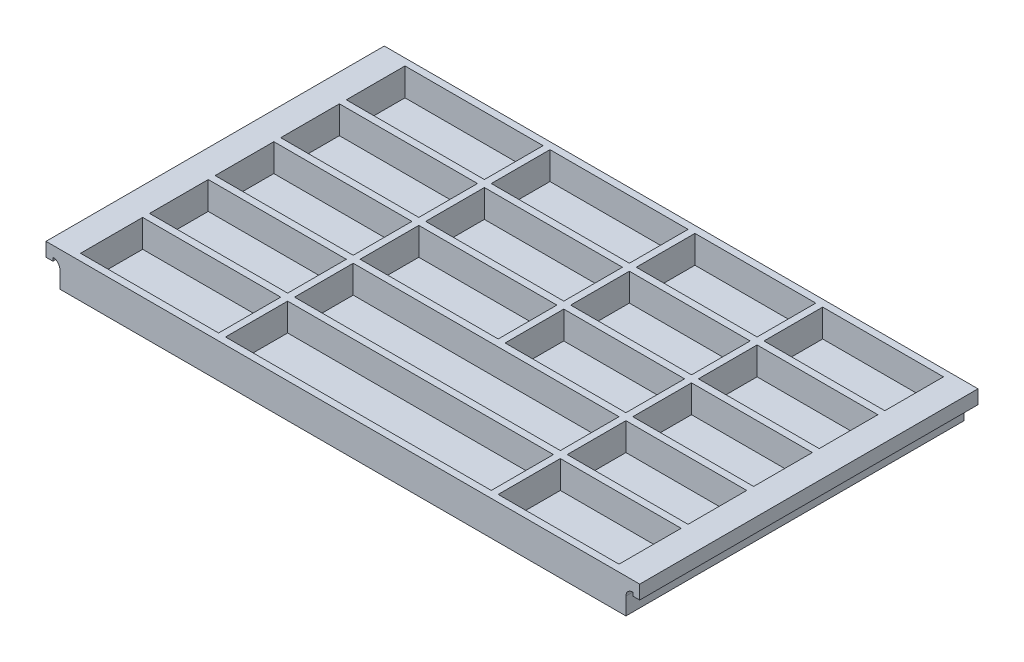
SolidWorks part; units mm, degrees
ref_plane "Front Plane" through (0, 0, 0) normal (0, 0, 1) x (1, 0, 0)
ref_plane "Top Plane" through (0, 0, 0) normal (0, 1, 0) x (1, 0, 0)
ref_plane "Right Plane" through (0, 0, 0) normal (1, 0, 0) x (0, 0, -1)
sketch "Sketch1" plane through (0, 0, 0) normal (0, 1, 0) x (1, 0, 0)
  line L1 (101.6, -62.23) -> (-101.6, -62.23)
  line L2 (101.6, -62.23) -> (101.6, 62.23)
  line L3 (101.6, 62.23) -> (-101.6, 62.23)
  line L4 (-101.6, -62.23) -> (-101.6, 62.23)
  line L5 (101.6, -62.23) -> (-101.6, 62.23) construction
  line L6 (101.6, 62.23) -> (-101.6, -62.23) construction
  line L32 (99.06, -59.69) -> (99.06, -36.83)
  line L37 (99.06, 59.69) -> (54.61, 59.69)
  line L39 (-99.06, -59.69) -> (-99.06, -36.83)
  line L41 (99.06, -59.69) -> (54.61, -59.69)
  line L42 (-48.26, 59.69) -> (-48.26, 38.1)
  line L45 (54.61, 59.69) -> (54.61, 38.1)
  line L46 (-99.06, 38.1) -> (-48.26, 38.1)
  line L51 (-99.06, 13.97) -> (-48.26, 13.97)
  line L53 (-44.4712, -27.2386) -> (-44.3417, -27.2342)
  line L54 (-99.06, -10.16) -> (-48.26, -10.16)
  line L55 (-99.06, -34.29) -> (-48.26, -34.29)
  line L56 (-45.72, 59.69) -> (-45.72, 38.1)
  line L57 (52.07, 59.69) -> (52.07, 38.1)
  line L60 (5.08, 59.69) -> (5.08, 38.1)
  line L61 (-99.06, 35.56) -> (-48.26, 35.56)
  line L62 (-99.06, 11.43) -> (-48.26, 11.43)
  line L63 (-99.06, -12.7) -> (-48.26, -12.7)
  line L64 (-99.06, -36.83) -> (-48.26, -36.83)
  line L66 (7.62, 59.69) -> (7.62, 38.1)
  line L71 (7.62, 35.56) -> (7.62, 13.97)
  line L73 (5.08, 35.56) -> (5.08, 13.97)
  line L76 (-48.26, 59.69) -> (-99.06, 59.69)
  line L78 (99.06, 59.69) -> (-99.06, 59.69) construction
  line L79 (-45.72, 35.56) -> (-45.72, 13.97)
  line L81 (-45.72, 59.69) -> (-45.72, -59.69) construction
  line L82 (-48.26, 35.56) -> (-48.26, 13.97)
  line L83 (5.08, 59.69) -> (-45.72, 59.69)
  line L84 (-48.26, 59.69) -> (-48.26, -59.69) construction
  line L85 (7.62, 38.1) -> (52.07, 38.1)
  line L86 (7.62, 35.56) -> (52.07, 35.56)
  line L87 (-99.06, 38.1) -> (99.06, 38.1) construction
  line L88 (-48.26, 11.43) -> (-48.26, -10.16)
  line L89 (-99.06, 35.56) -> (99.06, 35.56) construction
  line L90 (-45.72, 13.97) -> (5.08, 13.97)
  line L92 (-99.06, 13.97) -> (99.06, 13.97) construction
  line L93 (-45.72, 11.43) -> (-45.72, -10.16)
  line L94 (-45.72, 11.43) -> (5.08, 11.43)
  line L96 (-99.06, 11.43) -> (99.06, 11.43) construction
  line L97 (-99.06, 13.97) -> (-99.06, 35.56)
  line L99 (-99.06, -59.69) -> (-99.06, 59.69) construction
  line L100 (-99.06, 38.1) -> (-99.06, 59.69)
  line L101 (-99.06, -10.16) -> (-99.06, 11.43)
  line L102 (-45.72, -12.7) -> (-45.72, -34.29)
  line L103 (-45.72, -10.16) -> (5.08, -10.16)
  line L104 (-48.26, -12.7) -> (-48.26, -34.29)
  line L105 (-99.06, -10.16) -> (99.06, -10.16) construction
  line L106 (-45.72, -12.7) -> (5.08, -12.7)
  line L107 (-45.72, 35.56) -> (5.08, 35.56)
  line L108 (-99.06, -12.7) -> (99.06, -12.7) construction
  line L109 (-45.72, 38.1) -> (5.08, 38.1)
  line L110 (-45.72, -34.29) -> (5.08, -34.29)
  line L111 (-48.26, -36.83) -> (-48.26, -59.69)
  line L112 (-99.06, -34.29) -> (99.06, -34.29) construction
  line L113 (-45.72, -36.83) -> (-45.72, -59.69)
  line L114 (-45.72, -36.83) -> (52.07, -36.83)
  line L115 (-99.06, -34.29) -> (-99.06, -12.7)
  line L116 (-99.06, -36.83) -> (99.06, -36.83) construction
  line L117 (-48.26, -59.69) -> (-99.06, -59.69)
  line L118 (52.07, -59.69) -> (-45.72, -59.69)
  line L119 (99.06, -59.69) -> (-99.06, -59.69) construction
  line L120 (54.61, -36.83) -> (99.06, -36.83)
  line L121 (52.07, -36.83) -> (52.07, -59.69)
  line L122 (54.61, -36.83) -> (54.61, -59.69)
  line L123 (52.07, 59.69) -> (52.07, -59.69) construction
  line L124 (54.61, -34.29) -> (99.06, -34.29)
  line L125 (54.61, 59.69) -> (54.61, -59.69) construction
  line L126 (99.06, -34.29) -> (99.06, -12.7)
  line L127 (99.06, -10.16) -> (99.06, 11.43)
  line L128 (99.06, -59.69) -> (99.06, 59.69) construction
  line L129 (54.61, -12.7) -> (54.61, -34.29)
  line L130 (52.07, -12.7) -> (52.07, -34.29)
  line L131 (54.61, -10.16) -> (99.06, -10.16)
  line L132 (54.61, -12.7) -> (99.06, -12.7)
  line L133 (99.06, 13.97) -> (99.06, 35.56)
  line L134 (99.06, 38.1) -> (99.06, 59.69)
  line L135 (54.61, 35.56) -> (99.06, 35.56)
  line L136 (52.07, 35.56) -> (52.07, 13.97)
  line L137 (54.61, 35.56) -> (54.61, 13.97)
  line L138 (54.61, 38.1) -> (99.06, 38.1)
  line L139 (52.07, 59.69) -> (7.62, 59.69)
  line L140 (54.61, 13.97) -> (99.06, 13.97)
  line L141 (52.07, 11.43) -> (52.07, -10.16)
  line L142 (54.61, 11.43) -> (54.61, -10.16)
  line L143 (54.61, 11.43) -> (99.06, 11.43)
  line L144 (5.08, -12.7) -> (52.07, -12.7)
  line L145 (5.08, -34.29) -> (52.07, -34.29)
  line L146 (7.62, 13.97) -> (52.07, 13.97)
  line L147 (5.08, 11.43) -> (5.08, -10.16)
  line L148 (7.62, 11.43) -> (7.62, -10.16)
  line L149 (7.62, 11.43) -> (52.07, 11.43)
  line L150 (7.62, -10.16) -> (52.07, -10.16)
  point P0 (0, 0)
  point P6 (-109.855, 31.75)
  point P7 (109.855, 31.75)
  point P8 (-109.855, 1.27)
  point P9 (109.855, 1.27)
  point P10 (-109.855, -29.21)
  point P11 (109.855, -29.21)
  point P12 (-109.855, -26.67)
  point P13 (109.855, -26.67)
  point P14 (107.315, -59.69)
  point P15 (-107.315, -59.69)
  point P16 (-107.315, 59.69)
  point P17 (107.315, 59.69)
  point P18 (-109.855, 3.81)
  point P19 (109.855, 3.81)
  point P20 (-109.855, 34.29)
  point P21 (109.855, 34.29)
  point P74 (-66.675, 62.23)
  point P75 (-48.26, 34.29)
  point P80 (-64.135, 62.23)
  point P81 (-23.495, 62.23)
  point P86 (-23.495, 34.29)
  point P87 (19.685, 62.23)
  point P88 (19.685, 34.29)
  point P89 (62.865, 62.23)
  point P90 (54.61, 34.29)
  point P91 (-64.135, 34.29)
  point P92 (-20.955, 62.23)
  point P93 (-20.955, 34.29)
  point P94 (22.225, 62.23)
  point P95 (22.225, 34.29)
  point P96 (65.405, 62.23)
  point P97 (57.15, 38.1)
  dimension "D1" = 203.2
  dimension "D2" = 124.46
  dimension "D3" = 2.54
  dimension "D4" = 4
  dimension "D5" = 21.59
  dimension "D6" = 21.59
  dimension "D7" = 50.8
  dimension "D8" = 44.45
  dimension "D9" = 2.54
  dimension "D10" = 2.54
  dimension "D11" = 2.54
  dimension "D13" = 2.54
  dimension "D15" = 2.54
  dimension "D16" = 2.54
  dimension "D17" = 50.8
  dimension "D18" = 2.54
  dimension "D12" = 2.54
  dimension "D14" = 2.54
extrude "tray" add sketch "Sketch1" along normal blind 10.16
sketch "Sketch3" plane through (0, 0, 0) normal (0, -1, 0) x (-1, 0, 0)
  line L1 (-101.6, 62.23) -> (101.6, 62.23)
  line L2 (-101.6, 62.23) -> (-101.6, -62.23)
  line L3 (-101.6, -62.23) -> (101.6, -62.23)
  line L4 (101.6, 62.23) -> (101.6, -62.23)
  line L5 (-101.6, 62.23) -> (101.6, -62.23) construction
  line L6 (-101.6, -62.23) -> (101.6, 62.23) construction
  point P0 (0, 0)
extrude "base" add sketch "Sketch3" along normal blind 2.54
sketch "Sketch4" plane through (0, 0, 62.23) normal (0, 0, 1) x (1, 0, 0)
  line L0 (-101.6, -2.54) -> (-101.6, 10.16)
  line L1 (-101.6, 10.16) -> (-109.22, 10.16)
  line L2 (-109.22, 10.16) -> (-109.22, 5.08)
  line L4 (-101.6, -2.54) -> (-104.14, -2.54)
  line L5 (-104.14, -2.54) -> (-104.14, 3.81)
  line L6 (0, 70.2947) -> (0, -83.8304) construction
  line L7 (-106.68, 6.35) -> (-106.68, 5.08)
  line L8 (-106.68, 5.08) -> (-109.22, 5.08)
  line L9 (101.6, -2.54) -> (104.14, -2.54)
  line L10 (104.14, -2.54) -> (104.14, 3.81)
  line L11 (101.6, 10.16) -> (109.22, 10.16)
  line L12 (101.6, -2.54) -> (101.6, 10.16)
  line L13 (109.22, 10.16) -> (109.22, 5.08)
  line L14 (106.68, 5.08) -> (109.22, 5.08)
  line L15 (106.68, 6.35) -> (106.68, 5.08)
  arc A1 (-106.68, 6.35) -> (-104.14, 3.81) centre (-106.68, 3.81) cw
  arc A2 (106.68, 6.35) -> (104.14, 3.81) centre (106.68, 3.81) ccw
  dimension "D1" = 5.08
  dimension "D3" = 2.54
  dimension "D2" = 2.54
  dimension "D4" = 7.62
  dimension "D5" = 1.27
extrude "handle" add sketch "Sketch4" against normal up to surface (124.46 mm away) contours L2 L8 L7 A1 L5 L4 L0 L1 | L9 L10 A2 L15 L14 L13 L11 L12 up to face at (0, 3.81, -62.23)
